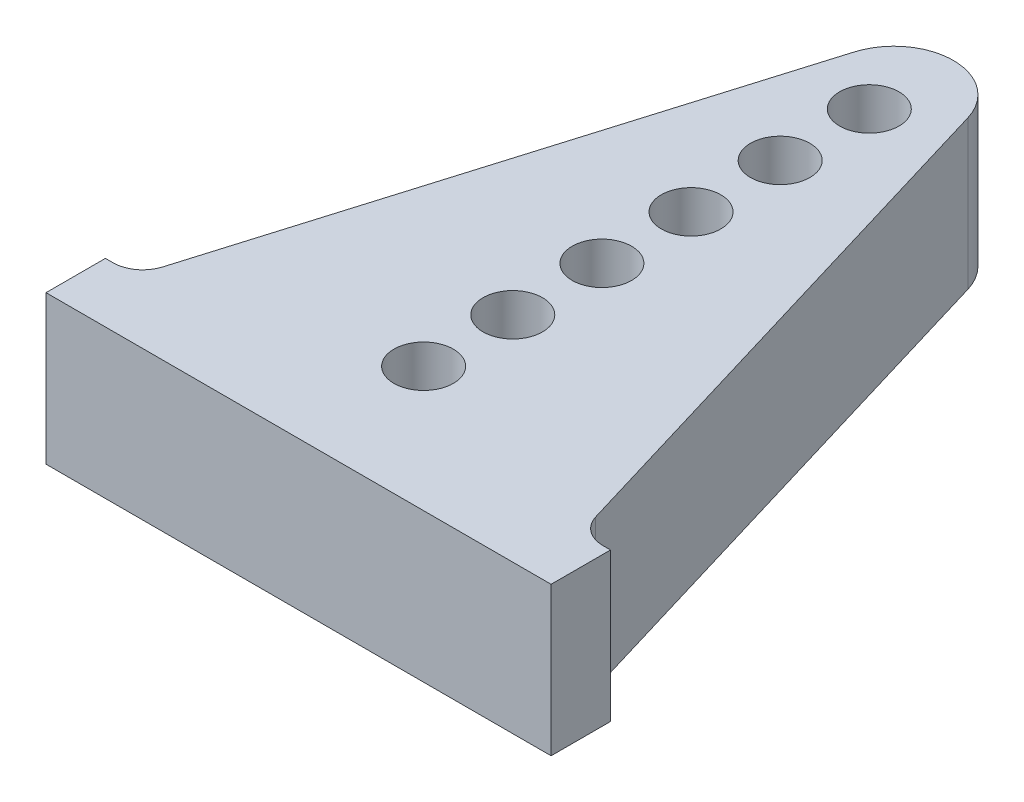
SolidWorks part; units mm, degrees
ref_plane "Front Plane" through (0, 0, 0) normal (0, 0, 1) x (1, 0, 0)
ref_plane "Top Plane" through (0, 0, 0) normal (0, 1, 0) x (1, 0, 0)
ref_plane "Right Plane" through (0, 0, 0) normal (1, 0, 0) x (0, 0, -1)
sketch "Sketch1" plane through (0, 0, 0) normal (0, 1, 0) x (1, 0, 0)
  line L0 (-8.2628, -4.7991) -> (-2.8922, 13.1027)
  line L1 (-8.4766, -5.5118) -> (6.5234, -5.5118)
  line L2 (-8.4766, -5.5118) -> (-8.4766, -7.5118)
  line L3 (-8.4766, -7.5118) -> (6.5234, -7.5118)
  line L4 (6.5234, -5.5118) -> (6.5234, -7.5118)
  line L5 (0.9391, 13.1027) -> (6.3096, -4.7991)
  line L7 (-9.4766, -5.5118) -> (-9.2206, -5.5118)
  line L8 (-9.4766, -5.5118) -> (-9.4766, -7.5118)
  line L9 (-9.4766, -7.5118) -> (-8.4766, -7.5118)
  line L10 (-8.4766, -5.5118) -> (-8.4766, -7.5118)
  line L11 (7.2675, -5.5118) -> (7.5234, -5.5118)
  line L12 (6.5234, -5.5118) -> (6.5234, -7.5118)
  line L13 (6.5234, -7.5118) -> (7.5234, -7.5118)
  line L14 (7.5234, -5.5118) -> (7.5234, -7.5118)
  circle A0 centre (-0.9766, 8.6983) radius 1
  circle A1 centre (-0.9766, 5.6983) radius 1
  circle A2 centre (-0.9766, 2.6983) radius 1
  circle A3 centre (-0.9766, -0.3017) radius 1
  circle A4 centre (-0.9766, -3.3017) radius 1
  arc A5 (0.9391, 13.1027) -> (-2.8922, 13.1027) centre (-0.9766, 12.528) ccw
  arc A6 (7.2675, -5.5118) -> (6.3096, -4.7991) centre (7.2675, -4.5118) cw
  arc A7 (-9.2206, -5.5118) -> (-8.2628, -4.7991) centre (-9.2206, -4.5118) ccw
  circle A8 centre (-0.9766, 11.6983) radius 1
  point P17 (-0.9766, 19.4882)
  dimension "D4" = 2
  dimension "D6" = 2
  dimension "D9" = 1
  dimension "D1" = 2
  dimension "D2" = 15
  dimension "D3" = 7.5
  dimension "D5" = 5
  dimension "D7" = 1
  dimension "D8" = 1
  dimension "D10" = 25
  dimension "D11" = 7.5
extrude "Boss-Extrude1" add sketch "Sketch1" along normal mid plane 5 contours A7 L7 L8 L9 L2 L1 L4 L13 L14 L11 A6 L5 A5 L0 A4 A3 A2 A1 A0 | L4 L1 L2 L3
equation "\"D3@Sketch1\"=(\"D2@Sketch1\")/2"
equation "\"D11@Sketch1\"=(\"D2@Sketch1\")/2"
